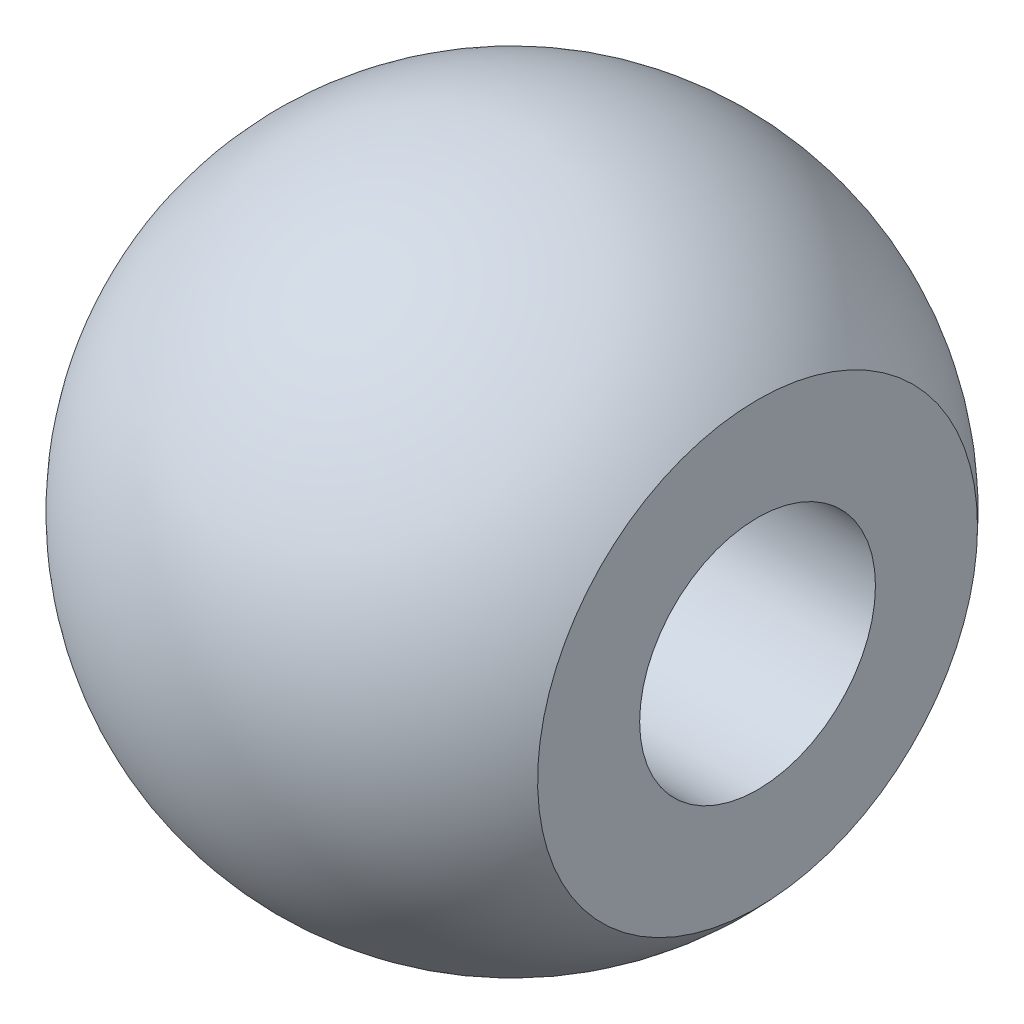
SolidWorks part; units mm, degrees
ref_plane "Front Plane" through (0, 0, 0) normal (0, 0, 1) x (1, 0, 0)
ref_plane "Top Plane" through (0, 0, 0) normal (0, 1, 0) x (1, 0, 0)
ref_plane "Right Plane" through (0, 0, 0) normal (1, 0, 0) x (0, 0, -1)
sketch "Sketch2" plane through (0, 0, 0) normal (0, 0, 1) x (1, 0, 0)
  line L0 (0, 0) -> (-15.0261, 0) construction
  line L1 (-7.1374, 0) -> (5.3161, 0)
  line L2 (5.3161, 0) -> (5.3161, 4.7625)
  arc A0 (-7.1374, 0) -> (5.3161, 4.7625) centre (0, 0) cw
  dimension "D1" = 14.2748
  dimension "D2" = 9.525
revolve "Revolve1" add sketch "Sketch2" angle 360 about L0
hole_wizard "1/4-20 Tapped Hole1" positions "Sketch3" profile "Sketch4" tap size "1/4-20" standard "ANSI Inch"
sketch "Sketch3" plane through (5.3161, 0, 0) normal (1, 0, 0) x (0, 0, -1)
  point P0 (0, 0)
sketch "Sketch4" plane through (5.3161, 0, 0) normal (0, 1, 0) x (0, 0, -1)
  line L0 (0, 0) -> (0, 10.4238)
  line L1 (0, 10.4238) -> (2.5527, 8.89)
  line L2 (2.5527, 8.89) -> (2.5527, 0)
  line L5 (2.5527, 0) -> (0, 0)
  line L10 (0, 10.4238) -> (-2.5527, 8.89) construction
  line L11 (0, -6.35) -> (0, 107.95) construction
  dimension "Tap Drill Dia." = 5.1054
  dimension "Tap Drill Depth" = 8.89
  dimension "Drill Angle" = 118
cosmetic thread "Hole Thread1" parameters "D1"=8.763, "D2"=6.35
